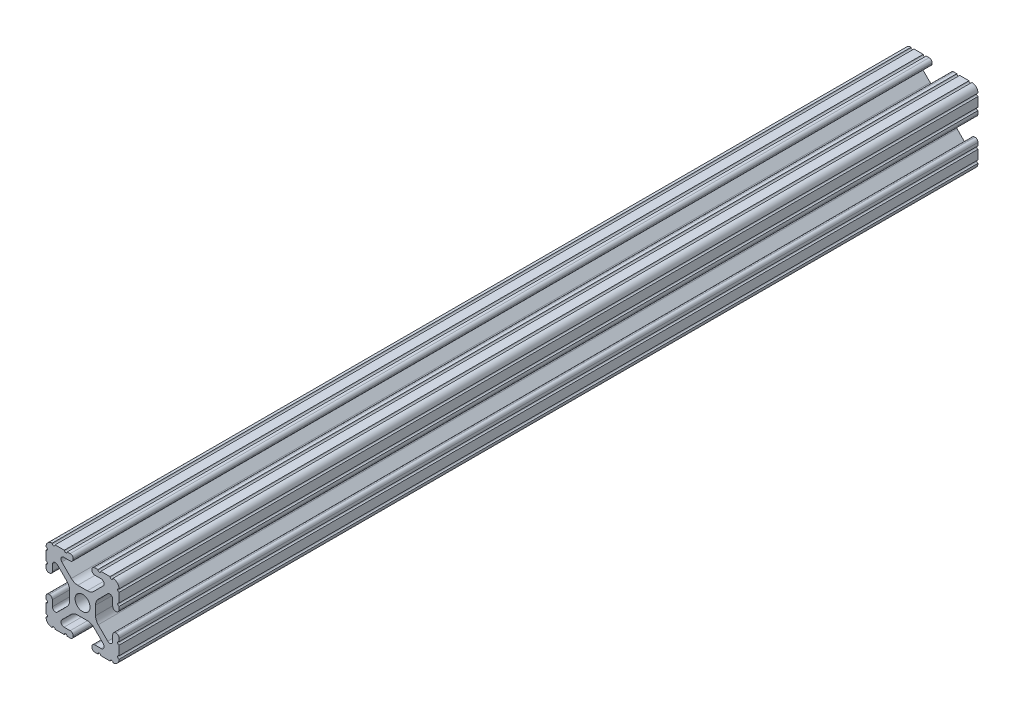
SolidWorks part; units mm, degrees
ref_plane "Front" through (0, 0, 0) normal (0, 0, 1) x (1, 0, 0)
ref_plane "Top" through (0, 0, 0) normal (0, 1, 0) x (1, 0, 0)
ref_plane "Right" through (0, 0, 0) normal (1, 0, 0) x (0, 0, -1)
sketch "Sketch1" plane through (0, 0, 0) normal (0, 0, 1) x (1, 0, 0)
  line L0 (-7.5107, 9.4563) -> (7.5107, 9.4563) construction
  line L1 (-7.4968, -9.4098) -> (7.4968, -9.4098) construction
  line L88 (-7.1797, -8.6452) -> (-3.9523, -5.4237)
  line L89 (-1.7093, -4.4958) -> (1.7093, -4.4958)
  line L90 (3.9523, -5.4237) -> (7.1797, -8.6452)
  line L91 (6.4164, -10.4902) -> (4.2875, -10.4902)
  line L92 (3.2385, -11.5392) -> (3.2385, -11.651)
  line L93 (4.2875, -12.7) -> (5.3171, -12.7)
  line L94 (6.3331, -12.7) -> (9.5504, -12.7)
  line L95 (12.7, -9.5504) -> (12.7, -6.3331)
  line L96 (12.7, -5.3171) -> (12.7, -4.2875)
  line L97 (11.651, -3.2385) -> (11.5392, -3.2385)
  line L98 (10.4902, -4.2875) -> (10.4902, -6.4021)
  line L99 (8.7371, -7.1294) -> (5.441, -3.8408)
  line L100 (4.5085, -1.5932) -> (4.5085, 1.5932)
  line L101 (5.441, 3.8408) -> (8.7371, 7.1294)
  line L102 (10.4902, 6.4021) -> (10.4902, 4.2875)
  line L103 (11.5392, 3.2385) -> (11.651, 3.2385)
  line L104 (12.7, 4.2875) -> (12.7, 5.3171)
  line L105 (12.7, 6.3331) -> (12.7, 9.5504)
  line L106 (9.5504, 12.7) -> (6.3331, 12.7)
  line L107 (5.3171, 12.7) -> (4.2875, 12.7)
  line L108 (3.2385, 11.651) -> (3.2385, 11.5392)
  line L109 (4.2875, 10.4902) -> (6.4768, 10.4902)
  line L110 (7.207, 8.7244) -> (3.8983, 5.4232)
  line L111 (1.6558, 4.4958) -> (-1.6558, 4.4958)
  line L112 (-3.8983, 5.4232) -> (-7.207, 8.7244)
  line L113 (-6.4768, 10.4902) -> (-4.2875, 10.4902)
  line L114 (-3.2385, 11.5392) -> (-3.2385, 11.651)
  line L115 (-4.2875, 12.7) -> (-5.3171, 12.7)
  line L116 (-6.3331, 12.7) -> (-9.5504, 12.7)
  line L117 (-12.7, 9.5504) -> (-12.7, 6.3331)
  line L118 (-12.7, 5.3171) -> (-12.7, 4.2875)
  line L119 (-11.651, 3.2385) -> (-11.5392, 3.2385)
  line L120 (-10.4902, 4.2875) -> (-10.4902, 6.4021)
  line L121 (-8.7371, 7.1294) -> (-5.441, 3.8408)
  line L122 (-4.5085, 1.5932) -> (-4.5085, -1.5932)
  line L123 (-5.441, -3.8408) -> (-8.7371, -7.1294)
  line L124 (-10.4902, -6.4021) -> (-10.4902, -4.2875)
  line L125 (-11.5392, -3.2385) -> (-11.651, -3.2385)
  line L126 (-12.7, -4.2875) -> (-12.7, -5.3171)
  line L127 (-12.7, -6.3331) -> (-12.7, -9.5504)
  line L128 (-9.5504, -12.7) -> (-6.3331, -12.7)
  line L129 (-5.3171, -12.7) -> (-4.2875, -12.7)
  line L130 (-3.2385, -11.651) -> (-3.2385, -11.5392)
  line L131 (-4.2875, -10.4902) -> (-6.4164, -10.4902)
  circle A1 centre (0, 0) radius 2.6035
  arc A104 (-7.1797, -8.6452) -> (-6.4164, -10.4902) centre (-6.4164, -9.4098) ccw
  arc A105 (-1.7093, -4.4958) -> (-3.9523, -5.4237) centre (-1.7093, -7.6708) ccw
  arc A106 (3.9523, -5.4237) -> (1.7093, -4.4958) centre (1.7093, -7.6708) ccw
  arc A107 (6.4164, -10.4902) -> (7.1797, -8.6452) centre (6.4164, -9.4098) ccw
  arc A108 (4.2875, -10.4902) -> (3.2385, -11.5392) centre (4.2875, -11.5392) ccw
  arc A109 (3.2385, -11.651) -> (4.2875, -12.7) centre (4.2875, -11.651) ccw
  arc A110 (6.3331, -12.7) -> (5.3171, -12.7) centre (5.8251, -12.7) ccw
  arc A111 (10.5664, -12.6998) -> (9.5504, -12.7) centre (10.0584, -12.7) ccw
  arc A112 (10.5664, -12.6998) -> (12.6998, -10.5664) centre (10.5918, -10.5918) ccw
  arc A113 (12.7, -9.5504) -> (12.6998, -10.5664) centre (12.7, -10.0584) ccw
  arc A114 (12.7, -5.3171) -> (12.7, -6.3331) centre (12.7, -5.8251) ccw
  arc A115 (12.7, -4.2875) -> (11.651, -3.2385) centre (11.651, -4.2875) ccw
  arc A116 (11.5392, -3.2385) -> (10.4902, -4.2875) centre (11.5392, -4.2875) ccw
  arc A117 (8.7371, -7.1294) -> (10.4902, -6.4021) centre (9.4628, -6.4021) ccw
  arc A118 (4.5085, -1.5932) -> (5.441, -3.8408) centre (7.6835, -1.5932) ccw
  arc A119 (5.441, 3.8408) -> (4.5085, 1.5932) centre (7.6835, 1.5932) ccw
  arc A120 (10.4902, 6.4021) -> (8.7371, 7.1294) centre (9.4628, 6.4021) ccw
  arc A121 (10.4902, 4.2875) -> (11.5392, 3.2385) centre (11.5392, 4.2875) ccw
  arc A122 (11.651, 3.2385) -> (12.7, 4.2875) centre (11.651, 4.2875) ccw
  arc A123 (12.7, 6.3331) -> (12.7, 5.3171) centre (12.7, 5.8251) ccw
  arc A124 (12.6998, 10.5664) -> (12.7, 9.5504) centre (12.7, 10.0584) ccw
  arc A125 (12.6998, 10.5664) -> (10.5664, 12.6998) centre (10.5918, 10.5918) ccw
  arc A126 (9.5504, 12.7) -> (10.5664, 12.6998) centre (10.0584, 12.7) ccw
  arc A127 (5.3171, 12.7) -> (6.3331, 12.7) centre (5.8251, 12.7) ccw
  arc A128 (4.2875, 12.7) -> (3.2385, 11.651) centre (4.2875, 11.651) ccw
  arc A129 (3.2385, 11.5392) -> (4.2875, 10.4902) centre (4.2875, 11.5392) ccw
  arc A130 (7.207, 8.7244) -> (6.4768, 10.4902) centre (6.4768, 9.4563) ccw
  arc A131 (1.6558, 4.4958) -> (3.8983, 5.4232) centre (1.6558, 7.6708) ccw
  arc A132 (-3.8983, 5.4232) -> (-1.6558, 4.4958) centre (-1.6558, 7.6708) ccw
  arc A133 (-6.4768, 10.4902) -> (-7.207, 8.7244) centre (-6.4768, 9.4563) ccw
  arc A134 (-4.2875, 10.4902) -> (-3.2385, 11.5392) centre (-4.2875, 11.5392) ccw
  arc A135 (-3.2385, 11.651) -> (-4.2875, 12.7) centre (-4.2875, 11.651) ccw
  arc A136 (-6.3331, 12.7) -> (-5.3171, 12.7) centre (-5.8251, 12.7) ccw
  arc A137 (-10.5664, 12.6998) -> (-9.5504, 12.7) centre (-10.0584, 12.7) ccw
  arc A138 (-10.5664, 12.6998) -> (-12.6998, 10.5664) centre (-10.5918, 10.5918) ccw
  arc A139 (-12.7, 9.5504) -> (-12.6998, 10.5664) centre (-12.7, 10.0584) ccw
  arc A140 (-12.7, 5.3171) -> (-12.7, 6.3331) centre (-12.7, 5.8251) ccw
  arc A141 (-12.7, 4.2875) -> (-11.651, 3.2385) centre (-11.651, 4.2875) ccw
  arc A142 (-11.5392, 3.2385) -> (-10.4902, 4.2875) centre (-11.5392, 4.2875) ccw
  arc A143 (-8.7371, 7.1294) -> (-10.4902, 6.4021) centre (-9.4628, 6.4021) ccw
  arc A144 (-4.5085, 1.5932) -> (-5.441, 3.8408) centre (-7.6835, 1.5932) ccw
  arc A145 (-5.441, -3.8408) -> (-4.5085, -1.5932) centre (-7.6835, -1.5932) ccw
  arc A146 (-10.4902, -6.4021) -> (-8.7371, -7.1294) centre (-9.4628, -6.4021) ccw
  arc A147 (-10.4902, -4.2875) -> (-11.5392, -3.2385) centre (-11.5392, -4.2875) ccw
  arc A148 (-11.651, -3.2385) -> (-12.7, -4.2875) centre (-11.651, -4.2875) ccw
  arc A149 (-12.7, -6.3331) -> (-12.7, -5.3171) centre (-12.7, -5.8251) ccw
  arc A150 (-12.6998, -10.5664) -> (-12.7, -9.5504) centre (-12.7, -10.0584) ccw
  arc A151 (-12.6998, -10.5664) -> (-10.5664, -12.6998) centre (-10.5918, -10.5918) ccw
  arc A152 (-9.5504, -12.7) -> (-10.5664, -12.6998) centre (-10.0584, -12.7) ccw
  arc A153 (-5.3171, -12.7) -> (-6.3331, -12.7) centre (-5.8251, -12.7) ccw
  arc A154 (-4.2875, -12.7) -> (-3.2385, -11.651) centre (-4.2875, -11.651) ccw
  arc A155 (-3.2385, -11.5392) -> (-4.2875, -10.4902) centre (-4.2875, -11.5392) ccw
extrude "Boss-Extrude1" add sketch "Sketch1" along normal mid plane 298.45
